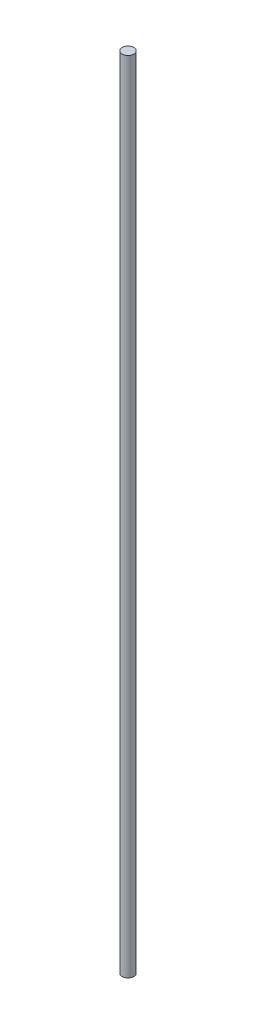
SolidWorks part; units mm, degrees
material "Chrome Stainless Steel"
ref_plane "Front Plane" through (0, 0, 0) normal (0, 0, 1) x (1, 0, 0)
ref_plane "Top Plane" through (0, 0, 0) normal (0, 1, 0) x (1, 0, 0)
ref_plane "Right Plane" through (0, 0, 0) normal (1, 0, 0) x (0, 0, -1)
sketch "Sketch1" plane through (0, 0, 0) normal (0, 1, 0) x (1, 0, 0)
  circle A0 centre (0, 0) radius 4
  dimension "D1" = 8
extrude "Boss-Extrude1" add sketch "Sketch1" along normal blind 550 contours A0
